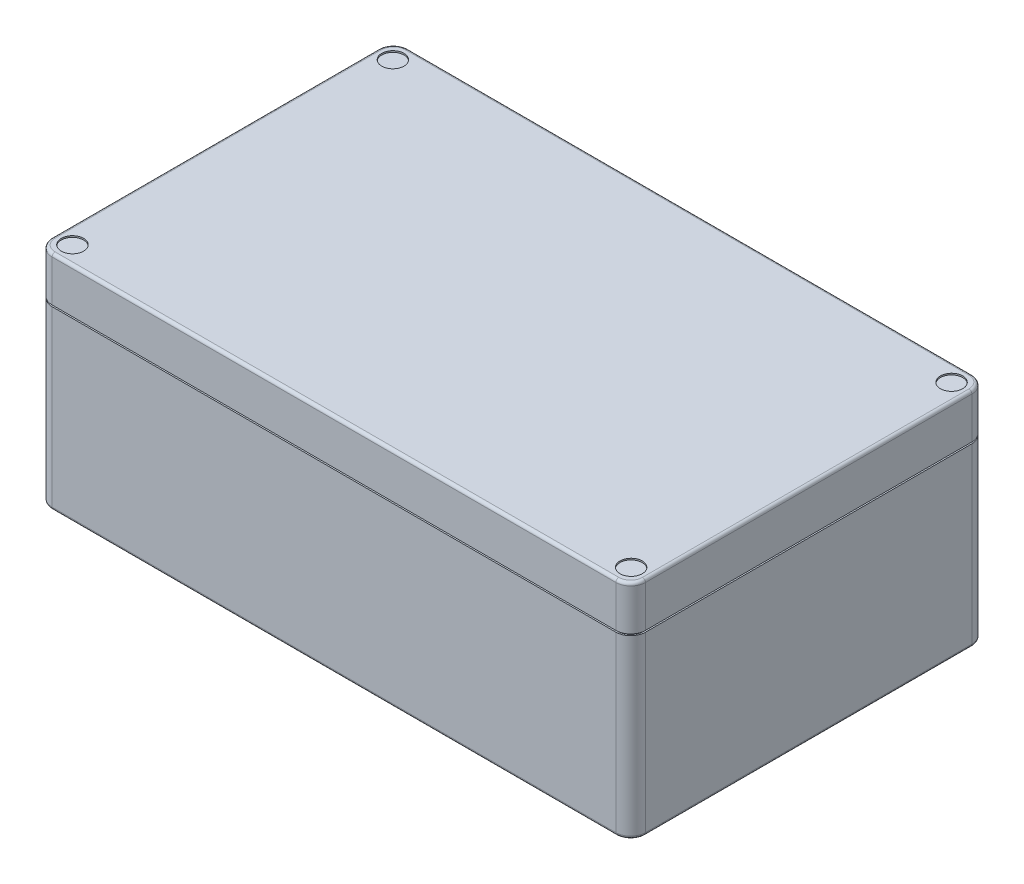
SolidWorks part; units mm, degrees
ref_plane "Front Plane" through (0, 0, 0) normal (0, 0, 1) x (1, 0, 0)
ref_plane "Top Plane" through (0, 0, 0) normal (0, 1, 0) x (1, 0, 0)
ref_plane "Right Plane" through (0, 0, 0) normal (1, 0, 0) x (0, 0, -1)
sketch "Sketch1" plane through (0, 0, 0) normal (0, 1, 0) x (1, 0, 0)
  line L1 (100, 60) -> (-100, 60)
  line L2 (100, 60) -> (100, -60)
  line L3 (100, -60) -> (-100, -60)
  line L4 (-100, 60) -> (-100, -60)
  line L5 (100, 60) -> (-100, -60) construction
  line L6 (100, -60) -> (-100, 60) construction
  point P0 (0, 0)
  dimension "D1" = 200
  dimension "D2" = 120
extrude "Boss-Extrude1" add sketch "Sketch1" along normal blind 75
ref_plane "Plane1" through (0, 60, 0) normal (0, 1, 0) x (1, 0, 0)
fillet "Fillet1" radius 5 4 edges at (-100, 37.5, -60) (100, 37.5, -60) (100, 37.5, 60) (-100, 37.5, 60)
sketch "Sketch3" plane through (0, 60, 0) normal (0, 1, 0) x (1, 0, 0)
  line L4 (95, 60) -> (-95, 60)
  line L5 (-100, 55) -> (-100, -55)
  line L6 (-95, -60) -> (95, -60)
  line L7 (100, -55) -> (100, 55)
  line L8 (95, 60) -> (-95, 60)
  line L9 (-100, 55) -> (-100, -55)
  line L10 (-95, -60) -> (95, -60)
  line L11 (100, -55) -> (100, 55)
  line L20 (95, 59.5) -> (-95, 59.5)
  line L21 (-99.5, 55) -> (-99.5, -55)
  line L22 (-95, -59.5) -> (95, -59.5)
  line L23 (99.5, -55) -> (99.5, 55)
  line L24 (95, 59.5) -> (-95, 59.5)
  line L25 (-99.5, 55) -> (-99.5, -55)
  line L26 (-95, -59.5) -> (95, -59.5)
  line L27 (99.5, -55) -> (99.5, 55)
  arc A4 (-95, 60) -> (-100, 55) centre (-95, 55) ccw
  arc A5 (-100, -55) -> (-95, -60) centre (-95, -55) ccw
  arc A6 (95, -60) -> (100, -55) centre (95, -55) ccw
  arc A7 (100, 55) -> (95, 60) centre (95, 55) ccw
  arc A8 (-95, 60) -> (-100, 55) centre (-95, 55) ccw
  arc A9 (-100, -55) -> (-95, -60) centre (-95, -55) ccw
  arc A10 (95, -60) -> (100, -55) centre (95, -55) ccw
  arc A11 (100, 55) -> (95, 60) centre (95, 55) ccw
  arc A20 (-95, 59.5) -> (-99.5, 55) centre (-95, 55) ccw
  arc A21 (-99.5, -55) -> (-95, -59.5) centre (-95, -55) ccw
  arc A22 (95, -59.5) -> (99.5, -55) centre (95, -55) ccw
  arc A23 (99.5, 55) -> (95, 59.5) centre (95, 55) ccw
  arc A24 (-95, 59.5) -> (-99.5, 55) centre (-95, 55) ccw
  arc A25 (-99.5, -55) -> (-95, -59.5) centre (-95, -55) ccw
  arc A26 (95, -59.5) -> (99.5, -55) centre (95, -55) ccw
  arc A27 (99.5, 55) -> (95, 59.5) centre (95, 55) ccw
  dimension "D1" = 0
  dimension "D2" = 0.5
extrude "Cut-Extrude2" cut sketch "Sketch3" against normal blind 0.5
sketch "Sketch4" plane through (0, 75, 0) normal (0, 1, 0) x (1, 0, 0)
  line L1 (94.15, -54) -> (-94.15, -54)
  line L2 (94.15, -54) -> (94.15, 54)
  line L3 (94.15, 54) -> (-94.15, 54)
  line L4 (-94.15, -54) -> (-94.15, 54)
  line L5 (94.15, -54) -> (-94.15, 54) construction
  line L6 (94.15, 54) -> (-94.15, -54) construction
  circle A0 centre (-94.15, 54) radius 3.75
  circle A1 centre (94.15, 54) radius 3.75
  circle A2 centre (94.15, -54) radius 3.75
  circle A3 centre (-94.15, -54) radius 3.75
  point P0 (0, 0)
  dimension "D3" = 7.5
  dimension "D1" = 108
  dimension "D2" = 188.3
extrude "Cut-Extrude3" cut sketch "Sketch4" against normal blind 0.5 contours A0 | A1 | A2 | A3
fillet "Fillet2" radius 1 16 edges at (-98.5355, 0, 58.5355) (-100, 0, 0) (-98.5355, 0, -58.5355) (0, 0, -60) (98.5355, 0, -58.5355) (100, 0, 0) (98.5355, 0, 58.5355) (-98.5355, 75, 58.5355) (-100, 75, 0) (-98.5355, 75, -58.5355) (0, 75, -60) (98.5355, 75, -58.5355) (100, 75, 0) (98.5355, 75, 58.5355) (0, 0, 60) (0, 75, 60)
